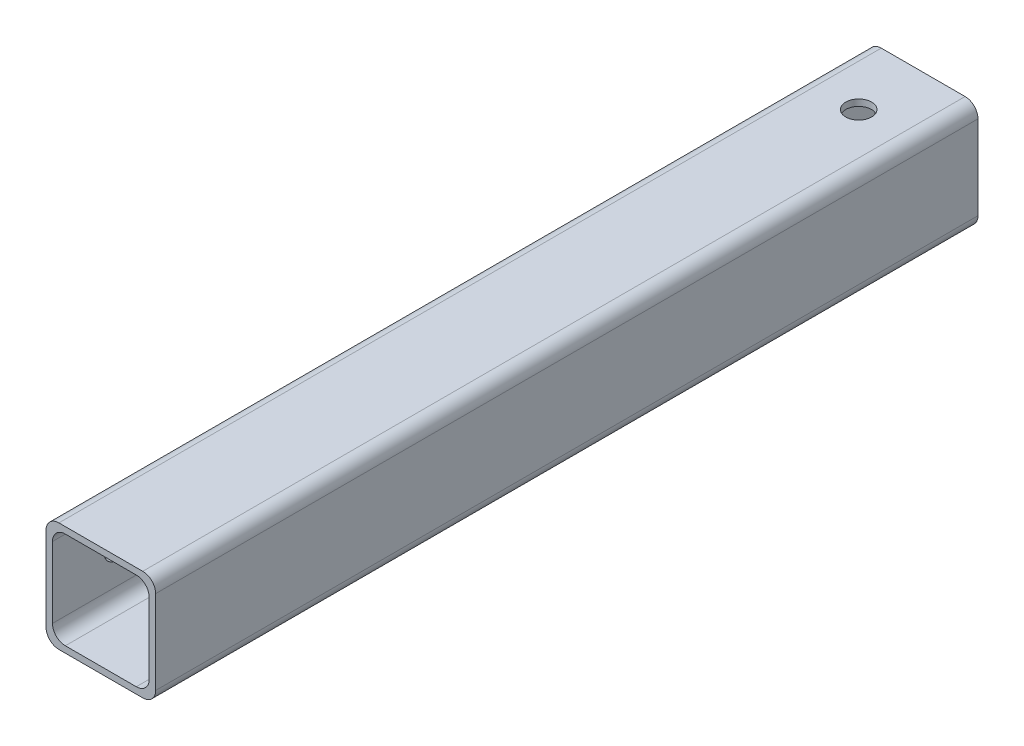
SolidWorks part; units mm, degrees
material "Hexcel AS4C (3000 Filaments)"
ref_plane "Front Plane" through (0, 0, 0) normal (0, 0, 1) x (1, 0, 0)
ref_plane "Top Plane" through (0, 0, 0) normal (0, 1, 0) x (1, 0, 0)
ref_plane "Right Plane" through (0, 0, 0) normal (1, 0, 0) x (0, 0, -1)
sketch "Sketch4" plane through (0, 0, 0) normal (0, 0, 1) x (1, 0, 0)
  line L1 (10.795, -10.795) -> (-10.795, -10.795)
  line L2 (10.795, -10.795) -> (10.795, 10.795)
  line L3 (10.795, 10.795) -> (-10.795, 10.795)
  line L4 (-10.795, -10.795) -> (-10.795, 10.795)
  line L5 (10.795, -10.795) -> (-10.795, 10.795) construction
  line L6 (10.795, 10.795) -> (-10.795, -10.795) construction
  line L7 (9.525, -9.525) -> (-9.525, -9.525)
  line L8 (9.525, -9.525) -> (9.525, 9.525)
  line L9 (9.525, 9.525) -> (-9.525, 9.525)
  line L10 (-9.525, -9.525) -> (-9.525, 9.525)
  line L11 (9.525, -9.525) -> (-9.525, 9.525) construction
  line L12 (9.525, 9.525) -> (-9.525, -9.525) construction
  point P0 (0, 0)
  point P1 (0, 0)
  dimension "D1" = 19.05
  dimension "D2" = 21.59
extrude "Boss-Extrude2" add sketch "Sketch4" along normal blind 161.925
sketch "Sketch5" plane through (10.795, 0, 0) normal (1, 0, 0) x (0, 0, -1)
  line L0 (-161.925, 10.795) -> (-156.594, -10.795)
  line L1 (-161.925, -10.795) -> (0, -10.795) construction
  line L2 (-156.594, -10.795) -> (-161.925, -10.795)
  line L3 (-161.925, -10.795) -> (-161.925, 10.795)
  dimension "D1" = 13.87
extrude "Cut-Extrude1" [suppressed] cut sketch "Sketch5" against normal through all
sketch "Sketch6" plane through (0, 0, 0) normal (1, 0, 0) x (0, 0, -1)
  line L0 (0, 0) -> (-76.2, 0)
  line L1 (-76.2, 0) -> (-414.3639, -193.2211)
  line L2 (-414.3639, -193.2211) -> (0, 0)
  dimension "D1" = 25
  dimension "D2" = 457.2
  dimension "D3" = 76.2
  dimension "D4" = 389.473
fillet "Fillet1" radius 2.54 8 edges at (10.795, 10.795, 80.9625) (10.795, -10.795, 80.9625) (-10.795, -10.795, 80.9625) (-10.795, 10.795, 80.9625) (-9.525, -9.525, 80.9625) (-9.525, 9.525, 80.9625) (9.525, 9.525, 80.9625) (9.525, -9.525, 80.9625)
sketch "Sketch7" plane through (0, 10.795, 0) normal (0, 1, 0) x (1, 0, 0)
  line L0 (0, 0) -> (0, -12.7) construction
  line L1 (8.255, 0) -> (-8.255, 0) construction
  point P3 (0, -12.7)
  dimension "D1" = 12.7
hole_wizard "#10 Clearance Hole1" positions "Sketch8" profile "Sketch9" hole size "#10" standard "ANSI Inch"
sketch "Sketch8" plane through (0, 10.795, 0) normal (0, 1, 0) x (1, 0, 0)
  point P0 (0, -12.7)
sketch "Sketch9" plane through (0, 10.795, 12.7) normal (1, 0, 0) x (0, 0, 1)
  line L0 (0, 0) -> (0, 14.2338)
  line L1 (0, 14.2338) -> (2.5527, 12.7)
  line L2 (2.5527, 12.7) -> (2.5527, 0)
  line L5 (2.5527, 0) -> (0, 0)
  line L10 (0, 14.2338) -> (-2.5527, 12.7) construction
  line L11 (0, -6.35) -> (0, 107.95) construction
  dimension "Hole Dia." = 5.1054
  dimension "Hole Depth" = 12.7
  dimension "Drill Angle" = 118
hole_wizard "#10 Clearance Hole2" positions "Sketch10" profile "Sketch11" hole size "#10" standard "ANSI Inch"
sketch "Sketch10" plane through (-10.795, 0, 0) normal (-1, 0, 0) x (0, 0, 1)
  line L1 (149.225, 8.255) -> (149.225, -8.255) construction
  line L2 (161.925, 8.255) -> (0, 8.255) construction
  line L3 (0, -8.255) -> (161.925, -8.255) construction
  line L8 (161.925, 8.255) -> (161.925, -8.255) construction
  point P0 (149.225, 0)
  point P20 (0, 0)
  point P21 (165.575, 13.0352)
  point P22 (165.1036, 10.6183)
  dimension "D1" = 12.7
sketch "Sketch11" plane through (-10.795, 0, 149.225) normal (0, 1, 0) x (0, 0, 1)
  line L0 (0, 0) -> (0, 14.2338)
  line L1 (0, 14.2338) -> (2.5527, 12.7)
  line L2 (2.5527, 12.7) -> (2.5527, 0)
  line L5 (2.5527, 0) -> (0, 0)
  line L10 (0, 14.2338) -> (-2.5527, 12.7) construction
  line L11 (0, -6.35) -> (0, 107.95) construction
  dimension "Hole Dia." = 5.1054
  dimension "Hole Depth" = 12.7
  dimension "Drill Angle" = 118
